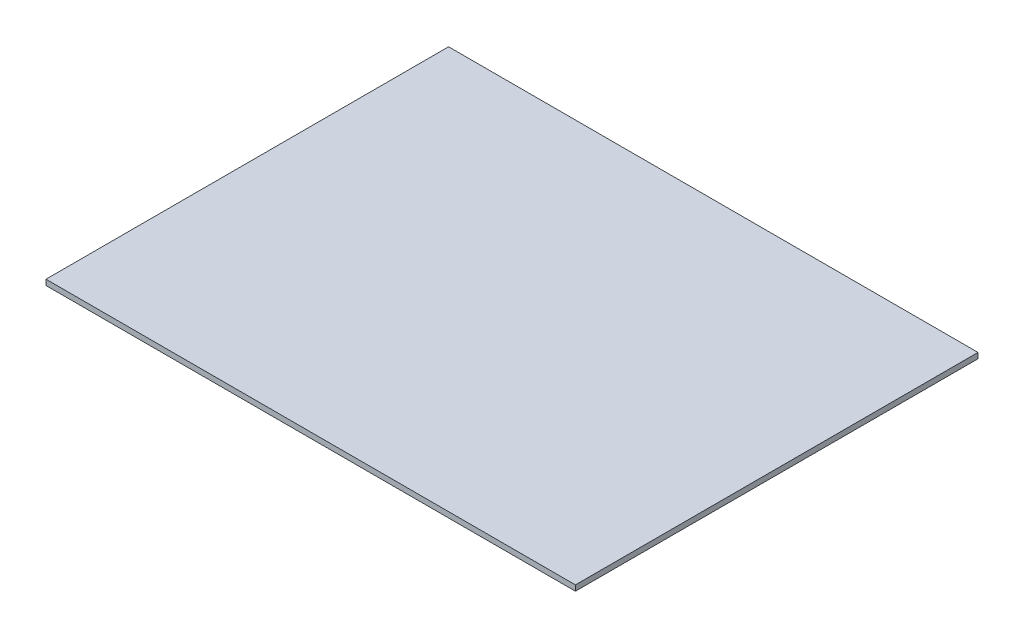
SolidWorks part; units mm, degrees
ref_plane "Front Plane" through (0, 0, 0) normal (0, 0, 1) x (1, 0, 0)
ref_plane "Top Plane" through (0, 0, 0) normal (0, 1, 0) x (1, 0, 0)
ref_plane "Right Plane" through (0, 0, 0) normal (1, 0, 0) x (0, 0, -1)
sketch "Sketch1" plane through (0, 0, 0) normal (0, 1, 0) x (1, 0, 0)
  line L1 (-243.84, 99.0051) -> (0, 99.0051)
  line L2 (-243.84, 99.0051) -> (-243.84, -86.4149)
  line L3 (-243.84, -86.4149) -> (0, -86.4149)
  line L4 (0, 99.0051) -> (0, -86.4149)
  dimension "D1" = 243.84
  dimension "D2" = 185.42
extrude "Boss-Extrude1" add sketch "Sketch1" along normal blind 2.54
